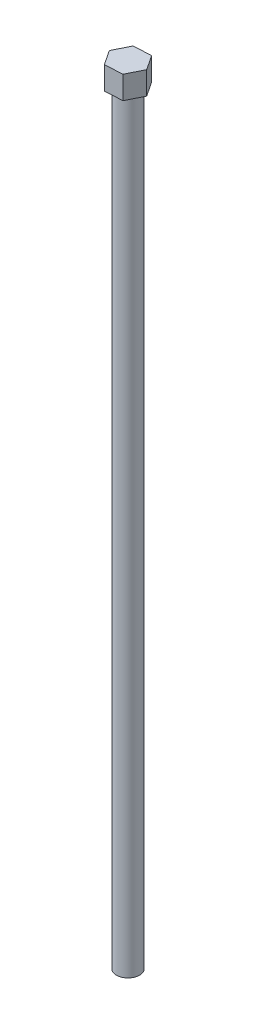
SolidWorks part; units mm, degrees
ref_plane "Front Plane" through (0, 0, 0) normal (0, 0, 1) x (1, 0, 0)
ref_plane "Top Plane" through (0, 0, 0) normal (0, 1, 0) x (1, 0, 0)
ref_plane "Right Plane" through (0, 0, 0) normal (1, 0, 0) x (0, 0, -1)
sketch "Sketch2" plane through (0, 0, 0) normal (0, 1, 0) x (1, 0, 0)
  circle A0 centre (0, 0) radius 1.5
  dimension "D1" = 3
extrude "Boss-Extrude1" add sketch "Sketch2" along normal blind 100
sketch "Sketch3" plane through (0, 100, 0) normal (0, 1, 0) x (1, 0, 0)
  line L1 (-2.3053, -0.1379) -> (-1.0332, -2.0654)
  line L2 (-1.0332, -2.0654) -> (1.2721, -1.9275)
  line L3 (1.2721, -1.9275) -> (2.3053, 0.1379)
  line L4 (2.3053, 0.1379) -> (1.0332, 2.0654)
  line L5 (1.0332, 2.0654) -> (-1.2721, 1.9275)
  line L6 (-1.2721, 1.9275) -> (-2.3053, -0.1379)
  circle A0 centre (0, 0) radius 2 construction
  dimension "D1" = 4
extrude "Boss-Extrude2" add sketch "Sketch3" along normal blind 3
